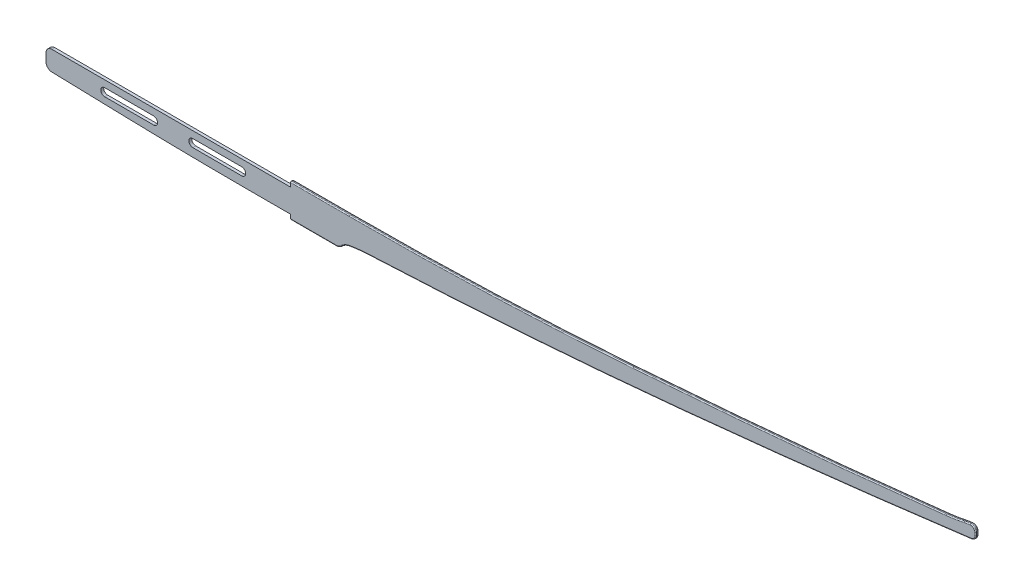
SolidWorks part; units mm, degrees
ref_plane "前视基准面" through (0, 0, 0) normal (0, 0, 1) x (1, 0, 0)
ref_plane "上视基准面" through (0, 0, 0) normal (0, 1, 0) x (1, 0, 0)
ref_plane "右视基准面" through (0, 0, 0) normal (1, 0, 0) x (0, 0, -1)
sketch "草图1" plane through (0, 0, 0) normal (0, 0, 1) x (1, 0, 0)
  line L0 (0, 43.7924) -> (0, -27.2669) construction
  line L1 (-61.6949, 0) -> (38.0085, 0) construction
  line L2 (0, 12) -> (-244, 12)
  line L3 (-250, 6) -> (-250, -2.1632)
  line L4 (-40, -12) -> (0, -12)
  line L5 (0, 12) -> (0, 17)
  line L7 (0, -12) -> (0, -17)
  line L9 (700, 305.6777) -> (700, 60.7138) construction
  line L10 (0, 17) -> (60, 17)
  line L11 (0, -17) -> (46.2642, -17)
  line L12 (700, 56.1674) -> (700, 53.1104)
  line L13 (700, 60.7138) -> (700, 56.1674) construction
  line L14 (700, 56.1674) -> (700, -973.6375) construction
  line L15 (700, 60.7138) -> (700, 56.1674) construction
  line L16 (-170, -10.2071) -> (-244.1655, -8.161)
  line L17 (-250, -8) -> (-250, -12) construction
  line L18 (-250, -12) -> (-40, -12) construction
  line L19 (-50, 1) -> (-100, 1) construction
  line L20 (-50, -3) -> (-100, -3)
  line L21 (-50, 5) -> (-100, 5)
  line L22 (-140, 1) -> (-190, 1) construction
  line L23 (-140, -3) -> (-190, -3)
  line L24 (-140, 5) -> (-190, 5)
  arc A18 (60, 17) -> (350, 27.5264) centre (60, 4017) ccw
  arc A19 (350, 27.5264) -> (670, 57.2599) centre (-230, 8006.4736) ccw
  arc A20 (51.9118, -14.6661) -> (60, -10.5) centre (62.501, -25.29) cw
  arc A21 (60, -10.5) -> (80, -8.3689) centre (87.3422, -172.1911) cw
  arc A22 (80, -8.3689) -> (400, 14.5587) centre (-188.6402, 5985.6141) ccw
  arc A23 (400, 14.5587) -> (695.6384, 48.1514) centre (-581.0669, 9966.3177) ccw
  arc A24 (700, 53.1104) -> (695.6384, 48.1514) centre (695, 53.1104) cw
  arc A25 (700, 56.1674) -> (694.6, 61.1514) centre (695, 56.1674) ccw
  arc A26 (694.6, 61.1514) -> (688, 60.188) centre (698.7169, 9.8551) ccw
  arc A27 (688, 60.188) -> (670, 57.2599) centre (648.8516, 244.052) cw
  arc A28 (670, 57.2599) -> (697.6068, 60.434) centre (-230, 8006.4736) ccw construction
  arc A29 (697.6068, 60.434) -> (700, 60.7138) centre (-230, 8006.4736) ccw construction
  arc A30 (-40, -12) -> (-170, -10.2071) centre (-40, 4701.8911) cw
  arc A31 (-244, 12) -> (-250, 6) centre (-244, 6) ccw
  arc A32 (-244.1655, -8.161) -> (-250, -2.1632) centre (-244, -2.1632) cw
  arc A33 (-50, -3) -> (-50, 5) centre (-50, 1) ccw
  arc A34 (-100, 5) -> (-100, -3) centre (-100, 1) ccw
  arc A35 (-140, -3) -> (-140, 5) centre (-140, 1) ccw
  arc A36 (-190, 5) -> (-190, -3) centre (-190, 1) ccw
  arc A37 (51.9118, -14.6661) -> (46.2642, -17) centre (46.2642, -9) cw
  point P29 (700, 48.7138)
  point P45 (-75, 1)
  point P54 (-165, 1)
  point P63 (50, -17)
  dimension "D10" = 80
  dimension "D11" = 300
  dimension "D12" = 6000
  dimension "D6" = 4000
  dimension "D8" = 8000
  dimension "D13" = 12
  dimension "D14" = 15
  dimension "D15" = 10000
  dimension "D18" = 5
  dimension "D19" = 5
  dimension "D27" = 6
  dimension "D35" = 8
  dimension "D1" = 250
  dimension "D2" = 24
  dimension "D3" = 60
  dimension "D4" = 34
  dimension "D5" = 700
  dimension "D7" = 50
  dimension "D9" = 350
  dimension "D16" = 60
  dimension "D17" = 10.5
  dimension "D20" = 30
  dimension "D21" = 12
  dimension "D22" = 5.4
  dimension "D23" = 13
  dimension "D24" = 4
  dimension "D25" = 80
  dimension "D26" = 40
  dimension "D28" = 50
  dimension "D29" = 50
  dimension "D30" = 1
  dimension "D31" = 8
  dimension "D32" = 40
  dimension "D33" = 50
  dimension "D34" = 8
extrude "凸台-拉伸1" add sketch "草图1" along normal mid plane 3
fillet "圆角1" radius 1 28 edges at (23.1321, -17, 1.5) (49.3196, -16.3935, 1.5) (55.6324, -11.955, 1.5) (69.9673, -9.1276, 1.5) (240.1533, 0.9557, 1.5) (547.9441, 30.2554, 1.5) (698.7544, 49.8083, 1.5) (700, 54.6389, 1.5) (698.3912, 59.8416, 1.5) (691.2844, 60.7767, 1.5) (679.0355, 58.5055, 1.5) (510.1493, 40.786, 1.5) (205.0955, 19.6325, 1.5) (23.1321, -17, -1.5) (49.3196, -16.3935, -1.5) (55.6324, -11.955, -1.5) (69.9673, -9.1276, -1.5) (30, 17, -1.5) (510.1493, 40.786, -1.5) (679.0355, 58.5055, -1.5) (691.2844, 60.7767, -1.5) (698.3912, 59.8416, -1.5) (700, 54.6389, -1.5) (698.7544, 49.8083, -1.5) (547.9441, 30.2554, -1.5) (30, 17, 1.5) (205.0955, 19.6325, -1.5) (240.1533, 0.9557, -1.5)
